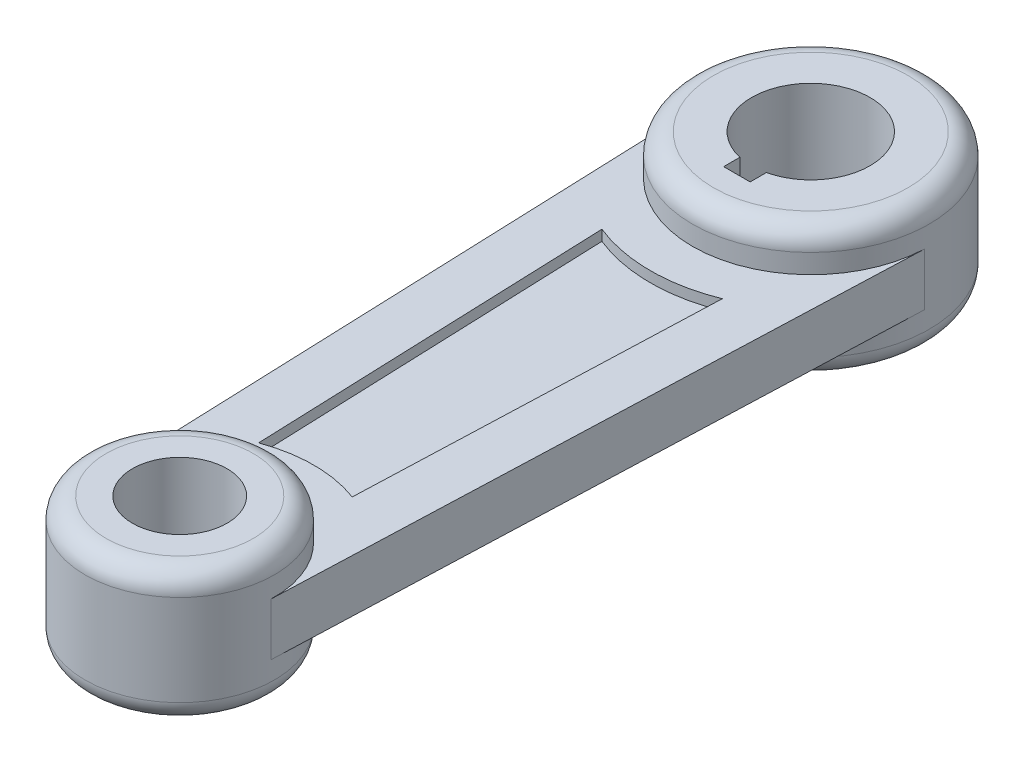
SolidWorks part; units mm, degrees
ref_plane "Front Plane" through (0, 0, 0) normal (0, 0, 1) x (1, 0, 0)
ref_plane "Top Plane" through (0, 0, 0) normal (0, 1, 0) x (1, 0, 0)
ref_plane "Right Plane" through (0, 0, 0) normal (1, 0, 0) x (0, 0, -1)
sketch "Sketch1" plane through (0, 0, 0) normal (0, 1, 0) x (1, 0, 0)
  circle A0 centre (0, 0) radius 45
  circle A1 centre (0, 0) radius 22.5
  circle A2 centre (0, 300) radius 56.25
  circle A3 centre (0, 300) radius 28.15
  dimension "D1" = 112.5
  dimension "D2" = 56.3
  dimension "D3" = 90
  dimension "D4" = 45
  dimension "D5" = 300
extrude "Boss-Extrude1" add sketch "Sketch1" along normal mid plane 63.3
sketch "Sketch2" plane through (0, 0, 0) normal (0, 1, 0) x (1, 0, 0)
  line L0 (56.2104, 297.8906) -> (44.9683, -1.6875)
  line L2 (-44.9683, -1.6875) -> (-56.2104, 297.8906)
  circle A0 centre (0, 0) radius 45 construction
  circle A1 centre (0, 300) radius 56.25 construction
  arc A2 (44.9683, -1.6875) -> (-44.9683, -1.6875) centre (0, 0) ccw
  arc A3 (-56.2104, 297.8906) -> (56.2104, 297.8906) centre (0, 300) ccw
extrude "Boss-Extrude2" add sketch "Sketch2" along normal mid plane 25
sketch "Sketch3" plane through (0, 12.5, 0) normal (0, 1, 0) x (1, 0, 0)
  line L2 (19.9859, -0.75) -> (31.228, 298.8281)
  line L3 (22.2559, 59.7389) -> (28.6198, 229.3249)
  line L5 (-31.228, 298.8281) -> (-19.9859, -0.75)
  line L6 (-28.6198, 229.3249) -> (-22.2559, 59.7389)
  arc A0 (-28.6198, 229.3249) -> (28.6198, 229.3249) centre (0, 300) ccw
  arc A1 (22.2559, 59.7389) -> (-22.2559, 59.7389) centre (0, 0) ccw
  dimension "D1" = 152.5
  dimension "D2" = 127.5
  dimension "D3" = 25
  dimension "D4" = 25
extrude "Cut-Extrude1" cut sketch "Sketch3" against normal blind 5
mirror "Mirror1" about plane through (0, 0, 0) normal (0, 1, 0) of "Cut-Extrude1"
sketch "Sketch4" plane through (0, 31.65, 0) normal (0, 1, 0) x (1, 0, 0)
  line L0 (0, 300) -> (0, 316.3179) construction
  line L2 (-6.3, 272.564) -> (-6.3, 264.864)
  line L3 (-6.3, 264.864) -> (6.3, 264.864)
  line L4 (6.3, 272.564) -> (6.3, 264.864)
  circle A0 centre (0, 300) radius 28.15 construction
  arc A1 (6.3, 272.564) -> (-6.3, 272.564) centre (0, 300) ccw
  dimension "D1" = 7.7
  dimension "D2" = 12.6
extrude "Cut-Extrude2" cut sketch "Sketch4" against normal through all
fillet "Fillet1" radius 10 4 edges at (0, -31.65, 45) (0, 31.65, 45) (0, -31.65, -243.75) (0, 31.65, -243.75)
